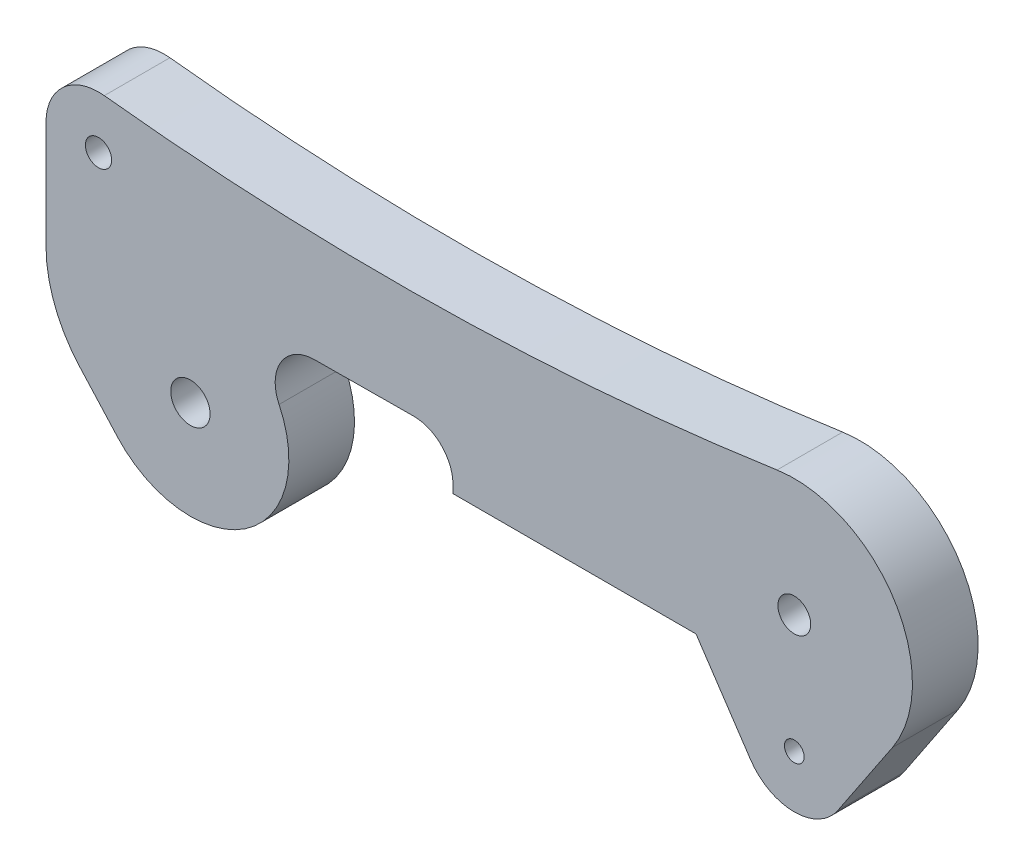
SolidWorks part; units mm, degrees
material "PMMA"
ref_plane "Front Plane" through (0, 0, 0) normal (0, 0, 1) x (1, 0, 0)
ref_plane "Top Plane" through (0, 0, 0) normal (0, 1, 0) x (1, 0, 0)
ref_plane "Right Plane" through (0, 0, 0) normal (1, 0, 0) x (0, 0, -1)
sketch "Sketch1" plane through (0, 0, 0) normal (0, 0, 1) x (1, 0, 0)
  line L0 (0, 0) -> (46, 0) construction
  line L1 (46, 0) -> (46, 9) construction
  line L2 (53.4833, 4) -> (49.3259, -2.2222)
  line L3 (42.6741, -2.2222) -> (38.5167, 4)
  line L4 (-11, 13) -> (-11, 4.8425)
  line L5 (-8.4269, -1.8538) -> (-5.5702, -5.0222)
  line L6 (38.5167, 4) -> (20, 4)
  line L7 (20, 4) -> (20, 4.6151)
  line L8 (16.9797, 7.615) -> (9.4359, 7.564)
  circle A0 centre (0, 0) radius 1.5
  circle A1 centre (46, 0) radius 0.75
  circle A2 centre (46, 9) radius 1.25
  circle A3 centre (-7, 13) radius 1
  arc A4 (-6.5594, 16.9757) -> (-11, 13) centre (-7, 13) ccw
  arc A6 (42.6741, -2.2222) -> (49.3259, -2.2222) centre (46, 0) ccw
  arc A7 (-5.5702, -5.0222) -> (6.7544, 3.2601) centre (0, 0) ccw
  arc A8 (-6.5594, 16.9757) -> (44.6854, 17.9035) centre (15.4723, 215.7585) ccw
  arc A9 (-8.4269, -1.8538) -> (-11, 4.8425) centre (-1, 4.8425) cw
  arc A10 (20, 4.6151) -> (16.9797, 7.615) centre (17, 4.6151) ccw
  arc A11 (6.7544, 3.2601) -> (9.4359, 7.564) centre (9.4562, 4.5641) cw
  arc A12 (53.4833, 4) -> (44.6854, 17.9035) centre (46, 9) ccw
  point P25 (-11, 1)
  dimension "D1" = 3
  dimension "D3" = 1.5
  dimension "D5" = 2.5
  dimension "D8" = 2
  dimension "D9" = 6.7544
  dimension "D10" = 8
  dimension "D11" = 8
  dimension "D12" = 15
  dimension "D13" = 200
  dimension "D15" = 10
  dimension "D17" = 3
  dimension "D18" = 3
  dimension "D2" = 46
  dimension "D4" = 9
  dimension "D6" = 7
  dimension "D7" = 13
  dimension "D14" = 12
  dimension "D16" = 20
  dimension "D19" = 4
  dimension "D20" = 17.9035
  dimension "D21" = 44.6854
  dimension "D22" = 53.4833
  dimension "D23" = 42.6741
extrude "Boss-Extrude1" add sketch "Sketch1" along normal blind 5
cosmetic thread "Cosmetic Thread2" parameters "D2"=3
cosmetic thread "Cosmetic Thread3" parameters "D2"=2
cosmetic thread "Cosmetic Thread4" parameters "D2"=2.5
